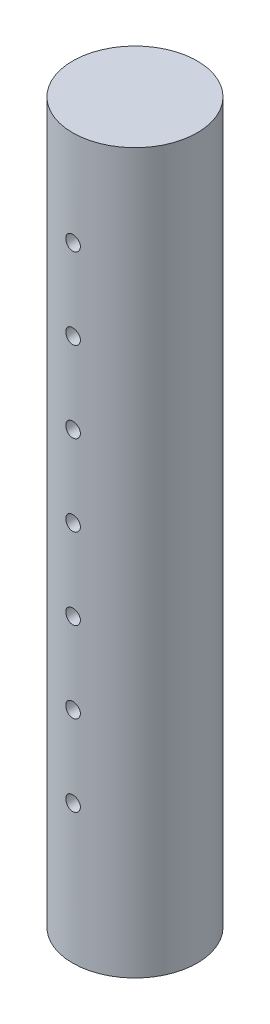
SolidWorks part; units mm, degrees
ref_plane "Front Plane" through (0, 0, 0) normal (0, 0, 1) x (1, 0, 0)
ref_plane "Top Plane" through (0, 0, 0) normal (0, 1, 0) x (1, 0, 0)
ref_plane "Right Plane" through (0, 0, 0) normal (1, 0, 0) x (0, 0, -1)
sketch "Sketch1" plane through (0, 0, 0) normal (0, 1, 0) x (1, 0, 0)
  circle A0 centre (0, 0) radius 3.85
  dimension "D1" = 7.7
extrude "Boss-Extrude1" add sketch "Sketch1" along normal blind 44.45
ref_plane "Plane1" through (0, 0, 5.08) normal (0, 0, 1) x (1, 0, 0)
sketch "Sketch4" plane through (0, 0, 5.08) normal (0, 0, 1) x (1, 0, 0)
  line L0 (0, -4.235) -> (0, 4.235) construction
  circle A0 centre (0, 8.5666) radius 0.45
  dimension "D1" = 0.9
extrude "Cut-Extrude1" cut sketch "Sketch4" against normal blind 10.16
pattern_linear "LPattern1" count 7 spacing 5 along (0, 1, 0) of "Cut-Extrude1"
